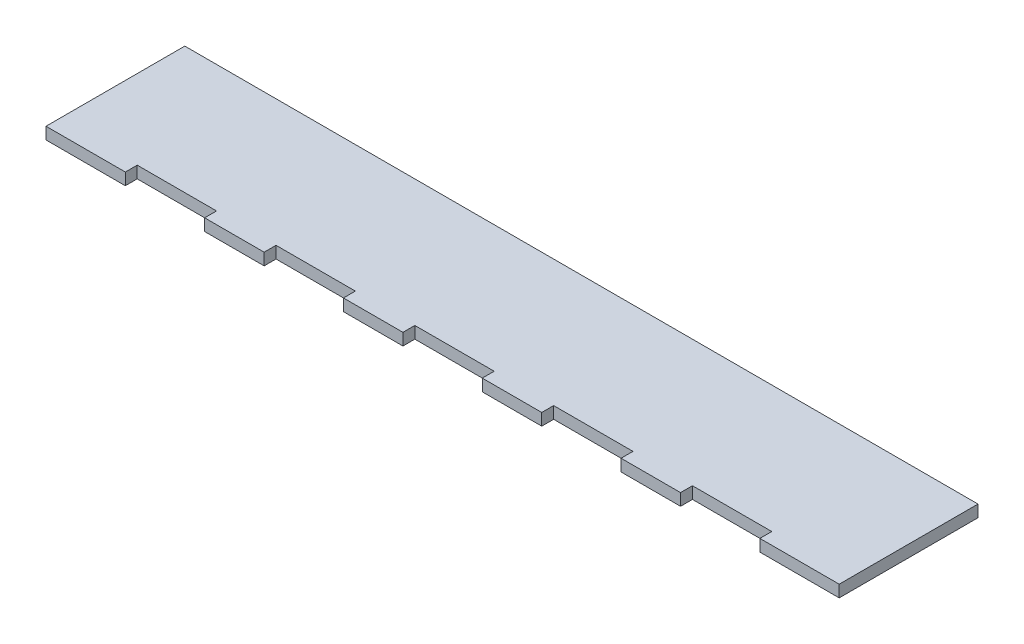
SolidWorks part; units mm, degrees
ref_plane "Front Plane" through (0, 0, 0) normal (0, 0, 1) x (1, 0, 0)
ref_plane "Top Plane" through (0, 0, 0) normal (0, 1, 0) x (1, 0, 0)
ref_plane "Right Plane" through (0, 0, 0) normal (1, 0, 0) x (0, 0, -1)
sketch "Sketch1" plane through (0, 0, 0) normal (0, 1, 0) x (1, 0, 0)
  line L0 (40, 0) -> (55, 0)
  line L1 (0, 0) -> (20, 0)
  line L2 (0, 0) -> (0, 35)
  line L3 (0, 35) -> (200, 35)
  line L4 (200, 0) -> (200, 35)
  line L5 (0, 0) -> (200, 35) construction
  line L6 (0, 35) -> (200, 0) construction
  line L7 (55, 3) -> (75, 3)
  line L8 (20, 0) -> (20, 3)
  line L9 (20, 3) -> (40, 3)
  line L10 (40, 0) -> (40, 3)
  line L11 (75, 0) -> (75, 3)
  line L12 (55, 0) -> (55, 3)
  line L13 (90, 3) -> (110, 3)
  line L14 (110, 0) -> (110, 3)
  line L15 (90, 0) -> (90, 3)
  line L16 (125, 3) -> (145, 3)
  line L17 (145, 0) -> (145, 3)
  line L18 (125, 0) -> (125, 3)
  line L19 (160, 3) -> (180, 3)
  line L20 (180, 0) -> (180, 3)
  line L21 (160, 0) -> (160, 3)
  line L22 (75, 0) -> (90, 0)
  line L23 (110, 0) -> (125, 0)
  line L24 (145, 0) -> (160, 0)
  line L25 (180, 0) -> (200, 0)
  point P4 (100, 17.5)
  point P10 (25.3866, 2.1907)
  dimension "D1" = 20
  dimension "D2" = 20
  dimension "D3" = 3
  dimension "D4" = 200
  dimension "D5" = 35
  dimension "D7" = 15
  dimension "D6" = 5
extrude "Boss-Extrude1" add sketch "Sketch1" along normal blind 3 contours L3 L4 L25 L20 L19 L21 L24 L17 L16 L18 L23 L14 L13 L15 L22 L11 L7 L12 L0 L10 L9 L8 L1 L2
